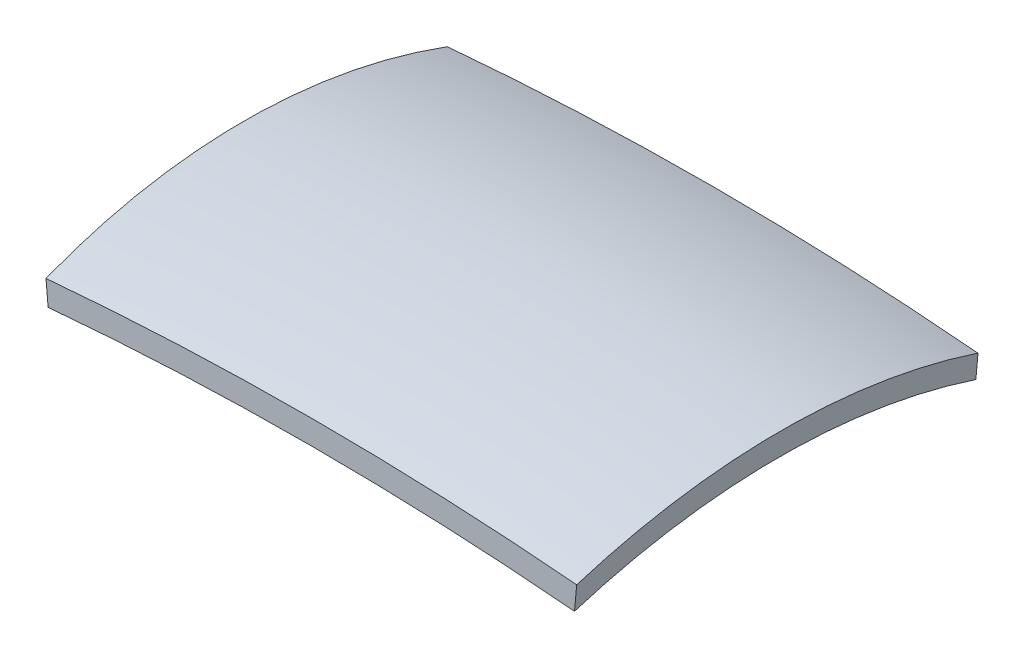
SolidWorks part; units mm, degrees
material "Alloy Steel"
ref_plane "Front Plane" through (0, 0, 0) normal (0, 0, 1) x (1, 0, 0)
ref_plane "Top Plane" through (0, 0, 0) normal (0, 1, 0) x (1, 0, 0)
ref_plane "Right Plane" through (0, 0, 0) normal (1, 0, 0) x (0, 0, -1)
sketch "Sketch1" plane through (0, 0, 0) normal (0, 0, 1) x (1, 0, 0)
  arc A0 (-381.3463, 0) -> (930.2537, 0) centre (274.4537, -7406.5232) cw
  dimension "D2" = 7435.5
  dimension "D1" = 1311.6
ref_plane "Plane1" through (-381.3463, 0, 0) normal (0.9961, 0.0882, 0) x (0, 0, -1)
sketch "Sketch2" plane through (-381.3463, 0, 0) normal (0.9961, 0.0882, 0) x (0, 0, -1)
  line L2 (1000, 0) -> (1000, 60)
  line L4 (0, 0) -> (0, 60)
  arc A0 (1000, 60) -> (0, 60) centre (500, -1354.2136) ccw
  arc A1 (1000, 0) -> (0, 0) centre (500, -1414.2136) ccw
  point P0 (0, 0)
  point P8 (492.4502, 60.043)
  point P9 (480.496, 9.2908)
  dimension "D3" = 1500
  dimension "D5" = 60
  dimension "D1" = 60
  dimension "D2" = 1000
  dimension "D4" = 60
sweep "Sweep1" add profiles "Sketch2" path "Sketch1"
